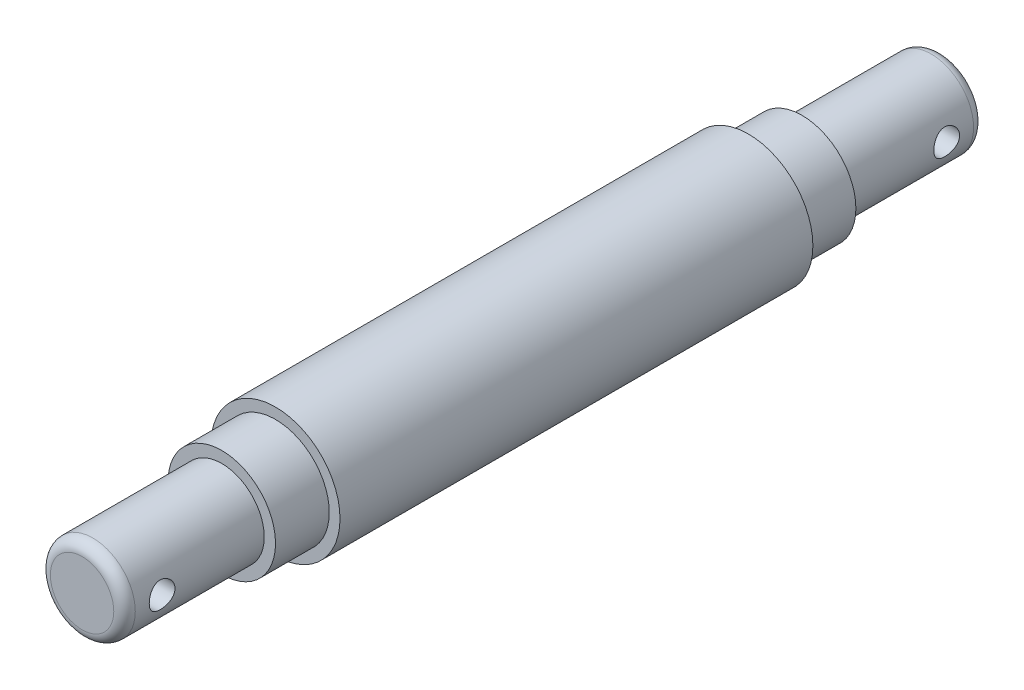
SolidWorks part; units mm, degrees
ref_plane "Front Plane" through (0, 0, 0) normal (0, 0, 1) x (1, 0, 0)
ref_plane "Top Plane" through (0, 0, 0) normal (0, 1, 0) x (1, 0, 0)
ref_plane "Right Plane" through (0, 0, 0) normal (1, 0, 0) x (0, 0, -1)
sketch "Sketch1" plane through (0, 0, 0) normal (0, 0, 1) x (1, 0, 0)
  circle A0 centre (0, 0) radius 3.95
  dimension "D1" = 7.9
extrude "Boss-Extrude1" add sketch "Sketch1" along normal blind 13
sketch "Sketch2" plane through (0, 0, 13) normal (0, 0, 1) x (1, 0, 0)
  circle A0 centre (0, 0) radius 5
  dimension "D1" = 10
extrude "Boss-Extrude2" add sketch "Sketch2" along normal blind 5
sketch "Sketch3" plane through (0, 0, 18) normal (0, 0, 1) x (1, 0, 0)
  circle A0 centre (0, 0) radius 6
  dimension "D1" = 12
extrude "Boss-Extrude3" add sketch "Sketch3" along normal blind 44
sketch "Sketch4" plane through (0, 0, 62) normal (0, 0, 1) x (1, 0, 0)
  circle A0 centre (0, 0) radius 5
  dimension "D1" = 10
extrude "Boss-Extrude4" add sketch "Sketch4" along normal blind 5
sketch "Sketch5" plane through (0, 0, 67) normal (0, 0, 1) x (1, 0, 0)
  circle A0 centre (0, 0) radius 3.95
  dimension "D1" = 7.9
extrude "Boss-Extrude5" add sketch "Sketch5" along normal blind 13
fillet "Fillet1" radius 1 2 edges at (3.95, 0, 80) (3.95, 0, 0)
sketch "Sketch6" plane through (0, 0, 0) normal (1, 0, 0) x (0, 0, -1)
  line L0 (-93.293, 0) -> (11.0779, 0) construction
  circle A0 centre (-76.5, 0) radius 1.2
  circle A1 centre (-3.5, 0) radius 1.2
  dimension "D1" = 2.4
  dimension "D3" = 2.4
  dimension "D2" = 2.5
  dimension "D4" = 2.5
extrude "Cut-Extrude1" cut sketch "Sketch6" against normal mid plane 13
